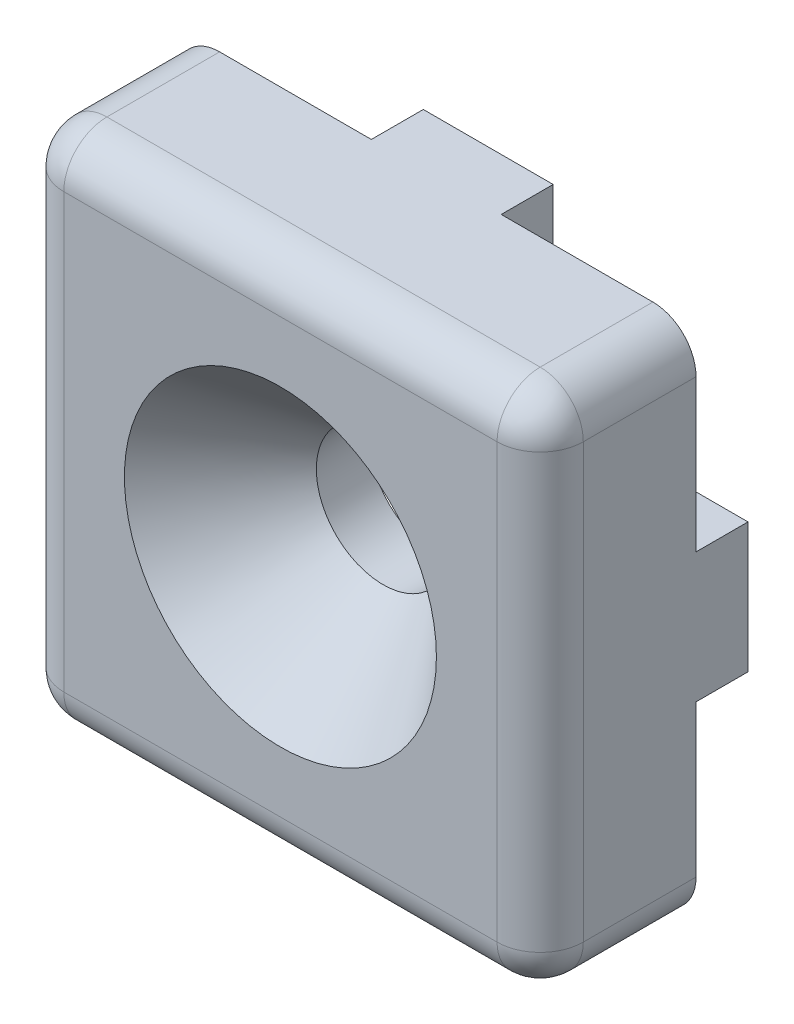
SolidWorks part; units mm, degrees
material "Custom Plastic"
ref_plane "Front Plane" through (0, 0, 0) normal (0, 0, 1) x (1, 0, 0)
ref_plane "Top Plane" through (0, 0, 0) normal (0, 1, 0) x (1, 0, 0)
ref_plane "Right Plane" through (0, 0, 0) normal (1, 0, 0) x (0, 0, -1)
sketch "Sketch1" plane through (0, 0, 0) normal (0, 0, 1) x (1, 0, 0)
  line L1 (-12.7, -12.7) -> (12.7, -12.7)
  line L2 (-12.7, -12.7) -> (-12.7, 12.7)
  line L3 (-12.7, 12.7) -> (12.7, 12.7)
  line L4 (12.7, -12.7) -> (12.7, 12.7)
  line L5 (-12.7, -12.7) -> (12.7, 12.7) construction
  line L6 (-12.7, 12.7) -> (12.7, -12.7) construction
  point P0 (0, 0)
  dimension "D1" = 25.4
extrude "Boss-Extrude1" add sketch "Sketch1" along normal mid plane 7.62
hole_wizard "CSK for 1/4 Flat Head Socket Cap Screw1" positions "Sketch2" profile "Sketch3" countersink size "1/4" standard "ANSI Inch" end condition through all
sketch "Sketch2" plane through (0, 0, 3.81) normal (0, 0, 1) x (1, 0, 0)
  point P0 (0, 0)
sketch "Sketch3" plane through (0, 0, 3.81) normal (1, 0, 0) x (0, -1, 0)
  line L0 (0, 0) -> (0, 7.62)
  line L1 (0, 7.62) -> (3.2639, 7.62)
  line L2 (3.2639, 7.62) -> (3.2639, 5.0191)
  line L3 (3.2639, 5.0191) -> (7.6269, 0)
  line L5 (7.6269, 0) -> (0, 0)
  line L6 (-3.2639, 5.0191) -> (-7.6269, 0) construction
  line L11 (0, -6.35) -> (0, 107.95) construction
  dimension "Thru Hole Dia." = 6.5278
  dimension "Thru Hole Depth" = 7.62
  dimension "Near C'Sink Dia." = 15.2538
  dimension "Near C'Sink Angle" = 82
fillet "Fillet1" radius 2.1082 8 edges at (-12.7, 0, 3.81) (0, 12.7, 3.81) (12.7, 0, 3.81) (0, -12.7, 3.81) (12.7, -12.7, 0) (-12.7, -12.7, 0) (12.7, 12.7, 0) (-12.7, 12.7, 0)
sketch "Sketch4" plane through (0, 0, -3.81) normal (0, 0, -1) x (-1, 0, 0)
  line L0 (0, 0) -> (-12.7, 0) construction
  line L1 (-12.7, -10.5918) -> (-12.7, 10.5918) construction
  line L2 (-3.175, 12.7) -> (3.175, 12.7)
  line L3 (-12.7, -3.175) -> (-10.16, -3.175)
  line L4 (-12.7, -3.175) -> (-12.7, 3.175)
  line L5 (-12.7, 3.175) -> (-10.16, 3.175)
  line L6 (-10.16, -3.175) -> (-10.16, 3.175)
  line L7 (-3.175, 12.7) -> (-3.175, 10.16)
  line L8 (-3.175, 10.16) -> (3.175, 10.16)
  line L9 (3.175, 12.7) -> (3.175, 10.16)
  line L10 (12.7, 3.175) -> (12.7, -3.175)
  line L11 (12.7, 3.175) -> (10.16, 3.175)
  line L12 (10.16, 3.175) -> (10.16, -3.175)
  line L13 (12.7, -3.175) -> (10.16, -3.175)
  line L14 (3.175, -12.7) -> (-3.175, -12.7)
  line L15 (3.175, -12.7) -> (3.175, -10.16)
  line L16 (3.175, -10.16) -> (-3.175, -10.16)
  line L17 (-3.175, -12.7) -> (-3.175, -10.16)
  dimension "D1" = 6.35
  dimension "D2" = 2.54
  dimension "D3" = 4
extrude "Boss-Extrude2" add sketch "Sketch4" along normal blind 2.54
